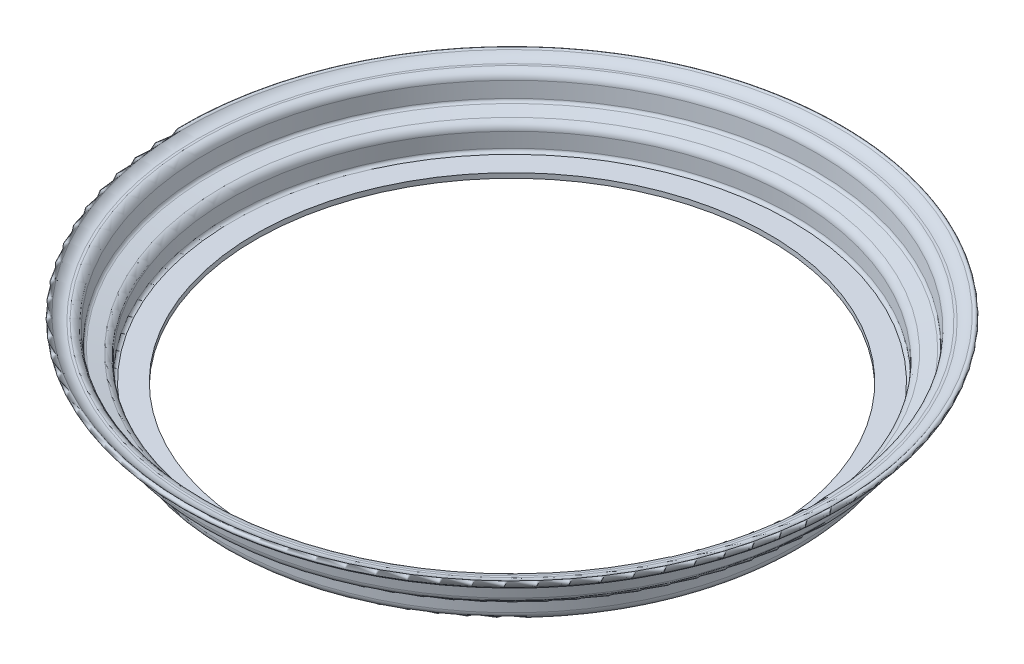
SolidWorks part; units mm, degrees
material "6061-T6 (SS)"
ref_plane "Front Plane" through (0, 0, 0) normal (0, 0, 1) x (1, 0, 0)
ref_plane "Top Plane" through (0, 0, 0) normal (0, 1, 0) x (1, 0, 0)
ref_plane "Right Plane" through (0, 0, 0) normal (1, 0, 0) x (0, 0, -1)
sketch "Sketch3" plane through (0, 0, 0) normal (0, 0, 1) x (1, 0, 0)
  line L0 (-167.2903, 0) -> (0, 0) construction
  line L2 (-202.8648, 33.0563) -> (-202.016, 23.3542)
  line L3 (-202.8648, 33.0563) -> (-202.8648, 23.7539) construction
  line L4 (-198.0181, 18.7578) -> (-189.6051, 16.8205)
  line L5 (-188.0539, 14.8715) -> (-188.0539, 5.18)
  line L6 (-188.0539, 0) -> (-168.1576, 0) construction
  line L7 (-182.8739, 0) -> (-168.1576, 0)
  line L8 (-168.1576, 3.175) -> (-168.1576, 0)
  line L9 (-199.7019, 33.333) -> (-198.8527, 23.6273)
  line L11 (-197.3091, 21.8526) -> (-188.8965, 19.9154)
  line L12 (-184.8789, 14.8675) -> (-184.8789, 5.175)
  line L13 (-182.8789, 3.175) -> (-168.1576, 3.175)
  line L14 (-184.8789, 18.9902) -> (-184.8789, 3.175) construction
  line L15 (-184.8789, 3.175) -> (-167.2903, 3.175) construction
  line L17 (-201.6878, 19.6028) -> (-188.0539, 16.4633) construction
  line L18 (-188.0539, 16.4633) -> (-188.0539, 0) construction
  line L25 (-204.8572, 38.057) -> (-206.3572, 38.057)
  line L26 (-206.3572, 34.882) -> (-204.8572, 34.882)
  line L36 (-199.7019, 33.333) -> (-198.726, 22.1789) construction
  line L37 (-198.726, 22.1789) -> (-184.8789, 18.9902) construction
  line L40 (-202.8648, 33.0563) -> (-201.6878, 19.6028) construction
  line L41 (0, 240.889) -> (0, -99.5724) construction
  line L44 (-188.0539, 0) -> (-167.2903, 0) construction
  line L63 (-201.8353, 37.083) -> (-201.8353, 37.083) construction
  line L64 (-201.8353, 37.083) -> (-201.8353, 37.083) construction
  arc A2 (-188.0539, 5.18) -> (-182.8739, 0) centre (-182.8739, 5.18) ccw
  arc A6 (-199.7019, 33.333) -> (-204.8572, 38.057) centre (-204.8572, 32.882) ccw
  arc A7 (-199.7019, 33.333) -> (-201.8353, 37.083) centre (-204.8572, 32.882) ccw construction
  arc A8 (-184.8789, 5.175) -> (-182.8789, 3.175) centre (-182.8789, 5.175) ccw
  arc A9 (-189.6051, 16.8205) -> (-188.0539, 14.8715) centre (-190.0539, 14.8715) cw
  arc A10 (-198.8527, 23.6273) -> (-197.3091, 21.8526) centre (-196.8603, 23.8016) ccw
  arc A11 (-188.8965, 19.9154) -> (-184.8789, 14.8675) centre (-190.0589, 14.8675) cw
  arc A12 (-202.016, 23.3542) -> (-198.0181, 18.7578) centre (-196.8557, 23.8057) ccw
  arc A24 (-202.8648, 33.0563) -> (-204.8572, 34.882) centre (-204.8572, 32.882) ccw
  arc A26 (-213.3101, 41.1399) -> (-215.6209, 39.0465) centre (-214.4655, 40.0932) ccw
  arc A27 (-213.3101, 41.1399) -> (-206.3572, 38.057) centre (-206.3572, 47.439) ccw
  arc A28 (-215.6209, 39.0465) -> (-206.3572, 34.882) centre (-206.3058, 47.3819) ccw
  arc A46 (-201.8353, 37.083) -> (-201.8353, 37.083) centre (-201.8353, 37.083) cw construction
  arc A47 (-201.8353, 37.083) -> (-201.8353, 37.083) centre (-201.8353, 37.083) ccw construction
  arc A48 (-201.8353, 37.083) -> (-201.8353, 37.083) centre (-201.8353, 37.083) ccw construction
  dimension "D5" = 2
  dimension "D6" = 2
  dimension "D4" = 5.175
  dimension "D7" = 5.18
  dimension "D9" = 5.18
  dimension "D2" = 5
  dimension "D3" = 3.175
revolve "Revolve2" add sketch "Sketch3" angle 360 about L41
